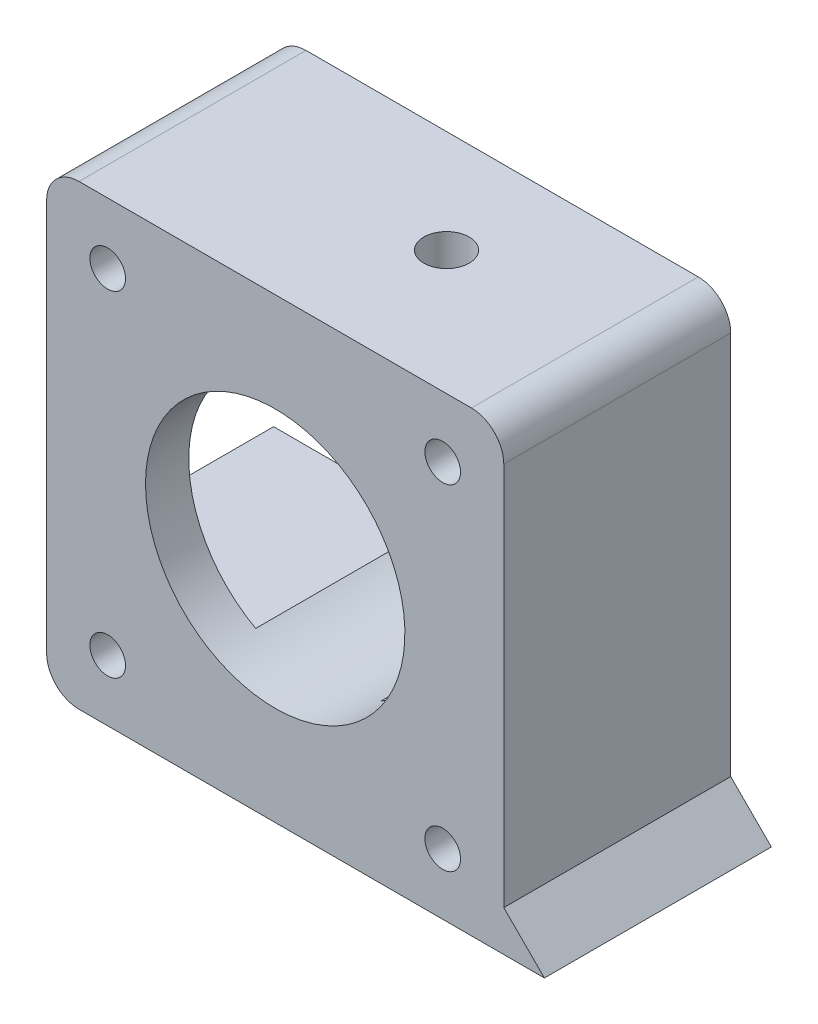
SolidWorks part; units mm, degrees
ref_plane "Ön Düzlem" through (0, 0, 0) normal (0, 0, 1) x (1, 0, 0)
ref_plane "Üst Düzlem" through (0, 0, 0) normal (0, 1, 0) x (1, 0, 0)
ref_plane "Sağ Düzlem" through (0, 0, 0) normal (1, 0, 0) x (0, 0, -1)
sketch "Çizim1" plane through (0, 0, 0) normal (0, 0, 1) x (1, 0, 0)
  line L0 (-6.9542, -22.0214) -> (-4.1258, -22.0214)
  line L1 (-24.04, 20.2786) -> (18.26, 20.2786)
  line L2 (-24.04, 20.2786) -> (-24.04, -22.0214)
  line L3 (7.5458, -22.0214) -> (10.3742, -22.0214)
  line L4 (18.26, 20.2786) -> (18.26, -18.2614)
  line L5 (10.3742, -22.0214) -> (18.26, -22.0214)
  line L6 (-6.9542, -22.0214) -> (-24.04, -22.0214)
  line L7 (-4.1258, -22.0214) -> (7.5458, -22.0214)
  line L9 (18.26, -18.2614) -> (22.02, -22.0214)
  line L10 (22.02, -22.0214) -> (18.26, -22.0214)
  circle A0 centre (-18.39, 14.6286) radius 1.65
  circle A1 centre (12.61, 14.6286) radius 1.65
  circle A2 centre (-18.39, -16.3714) radius 1.65
  circle A3 centre (12.61, -16.3714) radius 1.65
  dimension "D1" = 31
  dimension "D2" = 31
  dimension "D3" = 31
  dimension "D4" = 5.65
  dimension "D5" = 5.65
  dimension "D6" = 42.3
extrude "Yükseklik-Ekstrüzyon1" add sketch "Çizim1" along normal blind 21
fillet "Radyus1" radius 3 3 edges at (-24.04, 20.2786, 10.5) (18.26, 20.2786, 10.5) (-24.04, -22.0214, 10.5)
sketch "Çizim4" plane through (-24.04, 0, 0) normal (-1, 0, 0) x (0, 0, 1)
  line L3 (0, 9.6286) -> (17, 9.6286)
  line L4 (17, 9.6286) -> (17, -11.3714)
  line L6 (17, -11.3714) -> (0, -11.3714)
  line L7 (0, 9.6286) -> (0, -11.3714)
extrude "Kes-Ekstrüzyon3" cut sketch "Çizim4" against normal blind 40
sketch "Çizim5" plane through (0, 20.2786, 0) normal (0, 1, 0) x (1, 0, 0)
  line L0 (15.26, 0) -> (-21.04, 0) construction
  line L4 (18.26, 0) -> (18.26, -21) construction
  circle A0 centre (1.46, -9.5) radius 2.1
  dimension "D1" = 9.5
  dimension "D2" = 16.8
extrude "Kes-Ekstrüzyon4" cut sketch "Çizim5" against normal blind 55
sketch "Çizim2" plane through (0, 0, 0) normal (0, 0, -1) x (-1, 0, 0)
  circle A0 centre (2.89, -0.8714) radius 12
extrude "Kes-Ekstrüzyon1" cut sketch "Çizim2" against normal blind 23 and the other way blind 10
sketch "Çizim6" plane through (0, -22.0214, 0) normal (0, -1, 0) x (1, 0, 0)
  line L0 (-0.64, 9.5) -> (-0.64, 0)
  line L1 (-21.04, 0) -> (22.02, 0) construction
  line L2 (-0.64, 0) -> (3.56, 0)
  line L3 (3.56, 0) -> (3.56, 9.5)
  arc A0 (2.9195, 11.0099) -> (2.9195, 7.9901) centre (1.46, 9.5) ccw construction
  circle A1 centre (1.46, 9.5) radius 2.1 construction
  arc A2 (3.56, 9.5) -> (-0.64, 9.5) centre (1.46, 9.5) ccw
extrude "Kes-Ekstrüzyon5" cut sketch "Çizim6" against normal blind 15
